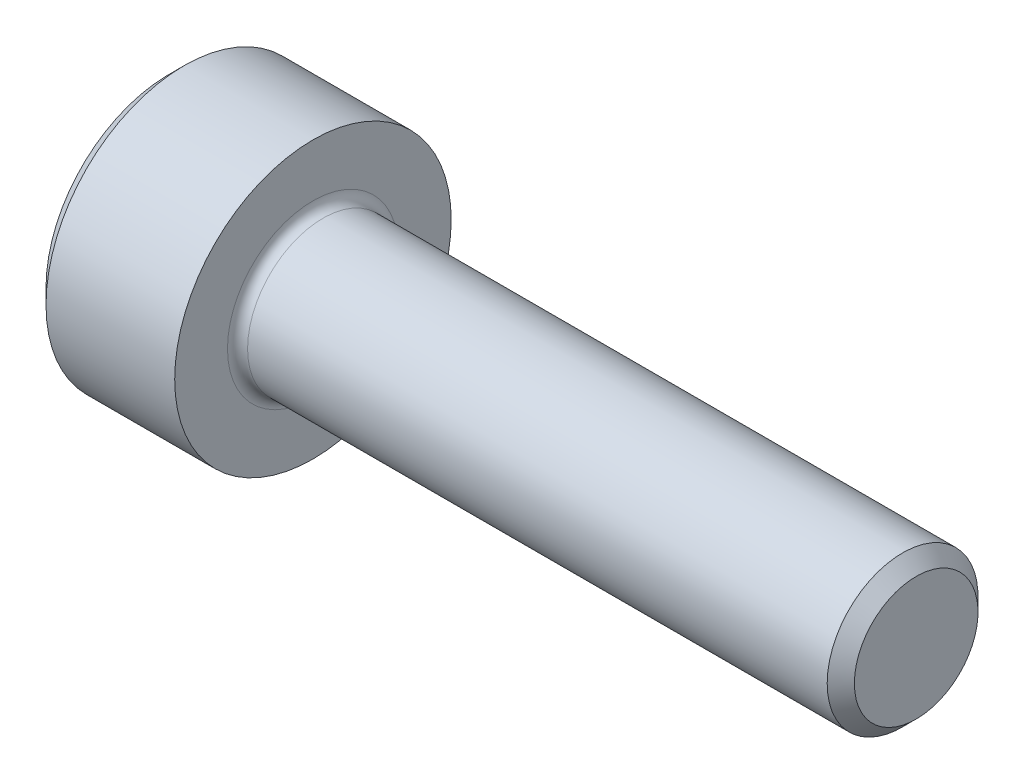
SolidWorks part; units mm, degrees
ref_plane "Front Plane" through (0, 0, 0) normal (0, 0, 1) x (1, 0, 0)
ref_plane "Top Plane" through (0, 0, 0) normal (0, 1, 0) x (1, 0, 0)
ref_plane "Right Plane" through (0, 0, 0) normal (1, 0, 0) x (0, 0, -1)
ref_plane "Plane1" through (0, 0, 0) normal (0, 0, 1) x (1, 0, 0)
sketch "Sketch1" plane through (0, 0, 0) normal (0, 0, 1) x (1, 0, 0)
  line L0 (-2.86, 0) -> (-2.86, 2.45)
  line L1 (-2.86, 2.45) -> (-2.56, 2.75)
  line L2 (-2.56, 2.75) -> (0, 2.75)
  line L3 (0, 2.75) -> (0, 1.7)
  line L4 (0.2, 1.5) -> (11.7295, 1.5)
  line L5 (11.7295, 1.5) -> (12, 1.2295)
  line L6 (12, 1.2295) -> (12, 0)
  line L7 (12, 0) -> (-2.86, 0)
  line L8 (12, 0) -> (-2.86, 0) construction
  arc A0 (0, 1.7) -> (0.2, 1.5) centre (0.2, 1.7) ccw
revolve "Revolve1" add sketch "Sketch1" angle 360 about L8
ref_plane "Plane2" through (-2.86, 0, 0) normal (1, 0, 0) x (0, 0, -1)
sketch "Sketch2" plane through (-2.86, 0, 0) normal (1, 0, 0) x (0, 0, -1)
  line L0 (-1.25, 0.7217) -> (-1.25, -0.7217)
  line L1 (-1.25, -0.7217) -> (0, -1.4434)
  line L2 (0, -1.4434) -> (1.25, -0.7217)
  line L3 (1.25, -0.7217) -> (1.25, 0.7217)
  line L4 (1.25, 0.7217) -> (0, 1.4434)
  line L5 (0, 1.4434) -> (-1.25, 0.7217)
extrude "Cut-Extrude1" cut sketch "Sketch2" along normal blind 1.3
ref_plane "Plane3" through (0, 0, 0) normal (0, 0, 1) x (1, 0, 0)
sketch "Sketch3" plane through (0, 0, 0) normal (0, 0, 1) x (1, 0, 0)
  line L0 (-1.56, 0) -> (-1.56, 1.25)
  line L1 (-1.56, 1.25) -> (-0.8383, 0)
  line L2 (-0.8383, 0) -> (-1.56, 0)
  line L3 (-0.8383, 0) -> (-1.56, 0) construction
revolve "Cut-Revolve1" cut sketch "Sketch3" angle 360 about L3
